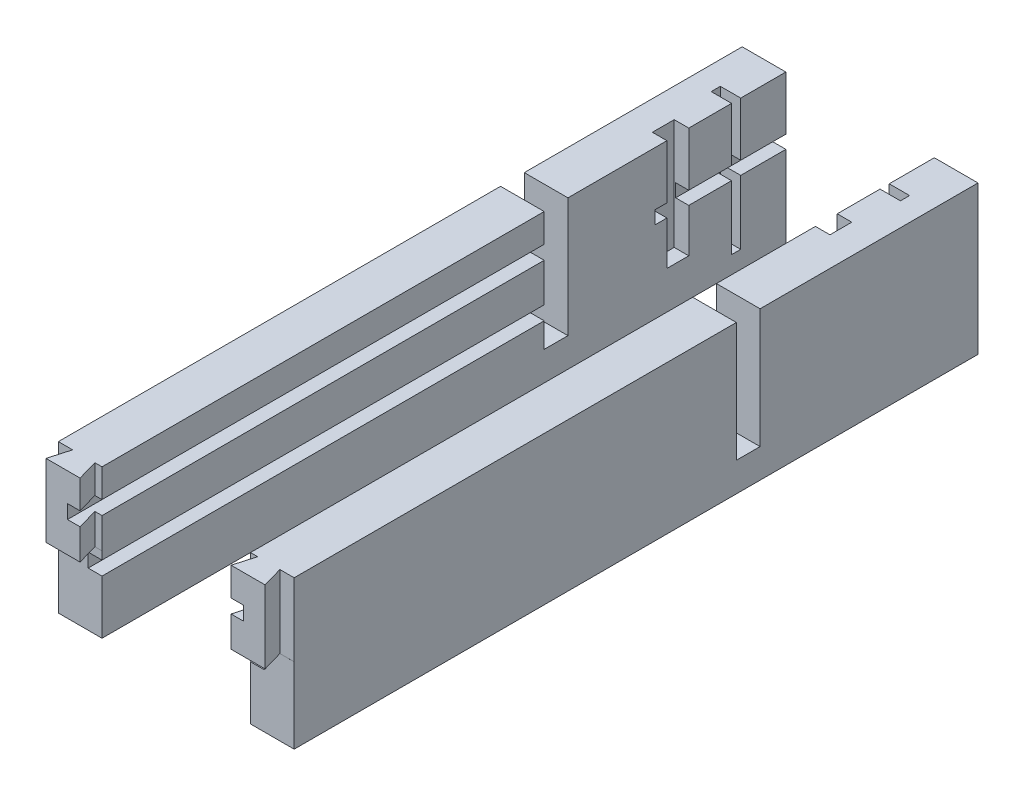
SolidWorks part; units mm, degrees
ref_plane "Front Plane" through (0, 0, 0) normal (0, 0, 1) x (1, 0, 0)
ref_plane "Top Plane" through (0, 0, 0) normal (0, 1, 0) x (1, 0, 0)
ref_plane "Right Plane" through (0, 0, 0) normal (1, 0, 0) x (0, 0, -1)
sketch "Sketch1" plane through (0, 0, 0) normal (1, 0, 0) x (0, 0, -1)
  line L1 (-64.5621, 30.5573) -> (177.4379, 30.5573)
  line L2 (-64.5621, 30.5573) -> (-64.5621, -20.4427)
  line L3 (-64.5621, -20.4427) -> (177.4379, -20.4427)
  line L4 (177.4379, 30.5573) -> (177.4379, -20.4427)
  dimension "D1" = 242
  dimension "D2" = 51
extrude "Boss-Extrude1" add sketch "Sketch1" along normal blind 15 contours L2 L3 L4 L1
sketch "Sketch12" plane through (0, 30.5573, 0) normal (0, 1, 0) x (1, 0, 0)
  line L0 (0, -57.4487) -> (4.9097, -57.4487)
  line L1 (0, -64.5621) -> (0, 177.4379) construction
  line L2 (4.9097, -57.4487) -> (2.87, -64.5621)
  line L3 (15, -64.5621) -> (0, -64.5621) construction
  line L4 (2.87, -64.5621) -> (0, -64.5621)
  line L5 (0, -64.5621) -> (0, -57.4487)
  line L6 (15, -57.4487) -> (15, -64.5621)
  line L7 (15, -64.5621) -> (15, 177.4379) construction
  line L8 (15, -64.5621) -> (14.57, -64.5621)
  line L9 (14.57, -64.5621) -> (12.5303, -57.4487)
  line L10 (12.5303, -57.4487) -> (15, -57.4487)
  dimension "D1" = 7.4
  dimension "D2" = 7.4
  dimension "D3" = 106
  dimension "D4" = 106
  dimension "D5" = 11.7
  dimension "D6" = 2.87
extrude "Cut-Extrude8" cut sketch "Sketch12" against normal blind 25
sketch "Sketch13" plane through (0, -20.4427, 0) normal (0, -1, 0) x (1, 0, 0)
  line L0 (15, 64.5621) -> (15, -177.4379) construction
  line L1 (0, 64.5621) -> (15, 64.5621)
  line L2 (0, 64.5621) -> (0, 57.4521)
  line L3 (0, 57.4521) -> (15, 57.4521)
  line L4 (15, 64.5621) -> (15, 57.4521)
  dimension "D1" = 7.11
extrude "Cut-Extrude9" cut sketch "Sketch13" against normal blind 26
sketch "Sketch17" plane through (0, 30.5573, 0) normal (0, 1, 0) x (1, 0, 0)
  line L0 (15, -57.4487) -> (15, 177.4379) construction
  line L1 (0, 110.4379) -> (15, 110.4379)
  line L2 (0, 110.4379) -> (0, 102.5879)
  line L3 (0, 102.5879) -> (15, 102.5879)
  line L4 (15, 110.4379) -> (15, 102.5879)
  line L6 (0, 102.5879) -> (15, 102.5879)
  line L7 (0, 102.5879) -> (0, 94.4379)
  line L8 (0, 94.4379) -> (15, 94.4379)
  line L9 (15, 102.5879) -> (15, 94.4379)
  line M14 (15, -57.4487) -> (15, 177.4379)
  line M16 (0, 177.4379) -> (0, -57.4487)
  dimension "D1" = 7.85
  dimension "D2" = 8.15
extrude "Cut-Extrude10" cut sketch "Sketch17" against normal blind 41 contours L8 L3 M16 M14
sketch "Sketch7" plane through (0, 0, -94.4379) normal (0, 0, -1) x (-1, 0, 0)
  line L0 (-15, -20.4427) -> (-15, -1.9427)
  line L1 (-15, 2.8073) -> (-15, 16.0573)
  line L2 (-10.25, 2.8073) -> (-15, 2.8073)
  line L3 (-10.25, 2.8073) -> (-10.25, -1.9427)
  line L4 (-10.25, -1.9427) -> (-15, -1.9427)
  line L5 (-15, 2.8073) -> (-15, -1.9427)
  line L6 (-15, 30.5573) -> (-15, -20.4427) construction
  line L8 (-15, 16.0573) -> (-10.25, 16.0573)
  line L9 (-15, 16.0573) -> (-15, 20.8073)
  line L10 (-15, 20.8073) -> (-10.25, 20.8073)
  line L11 (-10.25, 16.0573) -> (-10.25, 20.8073)
  dimension "D1" = 18.5
  dimension "D2" = 4.75
  dimension "D3" = 4.75
  dimension "D4" = 13.25
  dimension "D5" = 4.75
  dimension "D6" = 4.75
extrude "Cut-Extrude5" cut sketch "Sketch7" against normal blind 165
sketch "Sketch22" plane through (0, 30.5573, 0) normal (0, 1, 0) x (1, 0, 0)
  line L0 (15, 177.4379) -> (15, 161.9379)
  line L1 (15, 102.5879) -> (15, 177.4379) construction
  line L3 (15, 161.9379) -> (8, 161.9379)
  line L4 (15, 161.9379) -> (15, 158.7879)
  line L5 (15, 158.7879) -> (8, 158.7879)
  line L6 (8, 161.9379) -> (8, 158.7879)
  line M5 (15, 102.5879) -> (15, 177.4379)
  dimension "D1" = 15.5
  dimension "D2" = 7
  dimension "D3" = 3.15
extrude "Cut-Extrude13" cut sketch "Sketch22" against normal blind 45 contours L3 L6 L5 M5
ref_plane "Plane1" through (40.5, 0, 0) normal (1, 0, 0) x (0, 0, -1)
sketch "Sketch18" plane through (0, 30.5573, 0) normal (0, 1, 0) x (1, 0, 0)
  line L0 (15, 102.5879) -> (15, 136.5879)
  line L1 (15, 102.5879) -> (15, 158.7879) construction
  line L3 (15, 136.5879) -> (10, 136.5879)
  line L4 (15, 136.5879) -> (15, 144.0879)
  line L5 (15, 144.0879) -> (10, 144.0879)
  line L6 (10, 136.5879) -> (10, 144.0879)
  line M6 (15, 102.5879) -> (15, 158.7879)
  dimension "D1" = 34
  dimension "D2" = 5
  dimension "D3" = 7.5
extrude "Cut-Extrude11" cut sketch "Sketch18" against normal blind 38 contours L6 L3 L5 M6
sketch "Sketch23" plane through (0, 0, -177.4379) normal (0, 0, -1) x (-1, 0, 0)
  line L0 (-15, -20.4427) -> (-15, 7.5573)
  line L1 (-15, 30.5573) -> (-15, -20.4427) construction
  line L3 (-15, 7.5573) -> (-10.5, 7.5573)
  line L4 (-15, 7.5573) -> (-15, 12.0573)
  line L5 (-15, 12.0573) -> (-10.5, 12.0573)
  line L6 (-10.5, 7.5573) -> (-10.5, 12.0573)
  line M5 (-15, 30.5573) -> (-15, -20.4427)
  dimension "D1" = 4.5
  dimension "D2" = 4.5
extrude "Cut-Extrude14" cut sketch "Sketch23" against normal blind 45 contours L3 L6 L5 M5
mirror "Mirror4" about plane through (40.5, 0, 0) normal (1, 0, 0) of bodies 121 113
